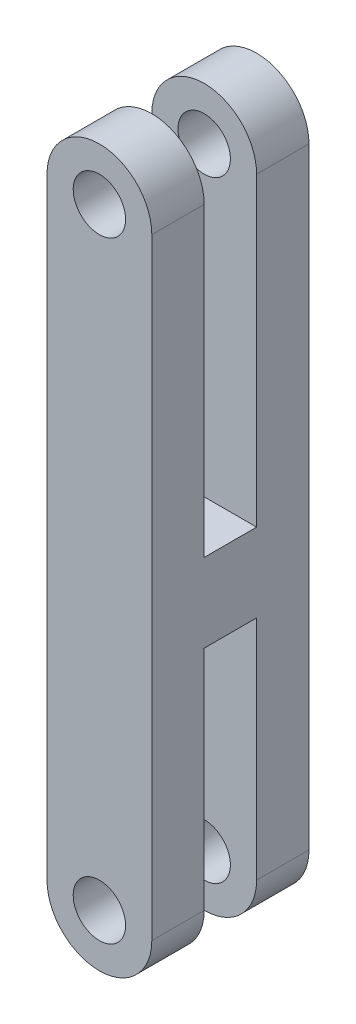
SolidWorks part; units mm, degrees
material "3.0205 (EN-AW 1200)"
ref_plane "Piano frontale" through (0, 0, 0) normal (0, 0, 1) x (1, 0, 0)
ref_plane "Piano superiore" through (0, 0, 0) normal (0, 1, 0) x (1, 0, 0)
ref_plane "Piano destro" through (0, 0, 0) normal (1, 0, 0) x (0, 0, -1)
sketch "Schizzo2" plane through (0, 0, 0) normal (0, 0, 1) x (1, 0, 0)
  line L0 (0, 0) -> (0, 35) construction
  line L1 (-3, 0) -> (-3, 35)
  line L2 (3, 0) -> (3, 35)
  arc A0 (-3, 0) -> (3, 0) centre (0, 0) ccw
  arc A1 (3, 35) -> (-3, 35) centre (0, 35) ccw
  circle A2 centre (0, 35) radius 1.5
  circle A4 centre (0, 0) radius 1.5
  point P3 (0, 17.5)
  dimension "D3" = 3
  dimension "D4" = 3
  dimension "D1" = 35
  dimension "D2" = 6
extrude "Estrusione-Estrusione1" add sketch "Schizzo2" along normal blind 9
sketch "Schizzo3" plane through (3, 0, 0) normal (1, 0, 0) x (0, 0, -1)
  line L0 (-3, 38) -> (-3, -3) construction
  line L3 (0, 38) -> (-9, 38) construction
  line L4 (-9, -3) -> (0, -3) construction
  line L5 (-6, 38) -> (-6, -3) construction
  line L6 (-9, 38) -> (-9, 35) construction
  dimension "D1" = 3
  dimension "D2" = 3
sketch "Schizzo5" plane through (3, 0, 0) normal (1, 0, 0) x (0, 0, -1)
  line L0 (-6, 38) -> (-6, 17.5)
  line L2 (-6, 38) -> (-6, -3) construction
  line L3 (-3, 38) -> (-3, 17.5)
  line L4 (-3, 38) -> (-3, -3) construction
  line L5 (-6, 17.5) -> (-3, 17.5)
  line L6 (-6, 38) -> (-3, 38)
  line L7 (-6, -3) -> (-6, 13)
  line L8 (-6, 13) -> (-3, 13)
  line L9 (-3, 13) -> (-3, -3)
  line L10 (-3, -3) -> (-6, -3)
  dimension "D1" = 20.5
  dimension "D2" = 16
extrude "Taglio-Estrusione1" cut sketch "Schizzo5" against normal blind 15
